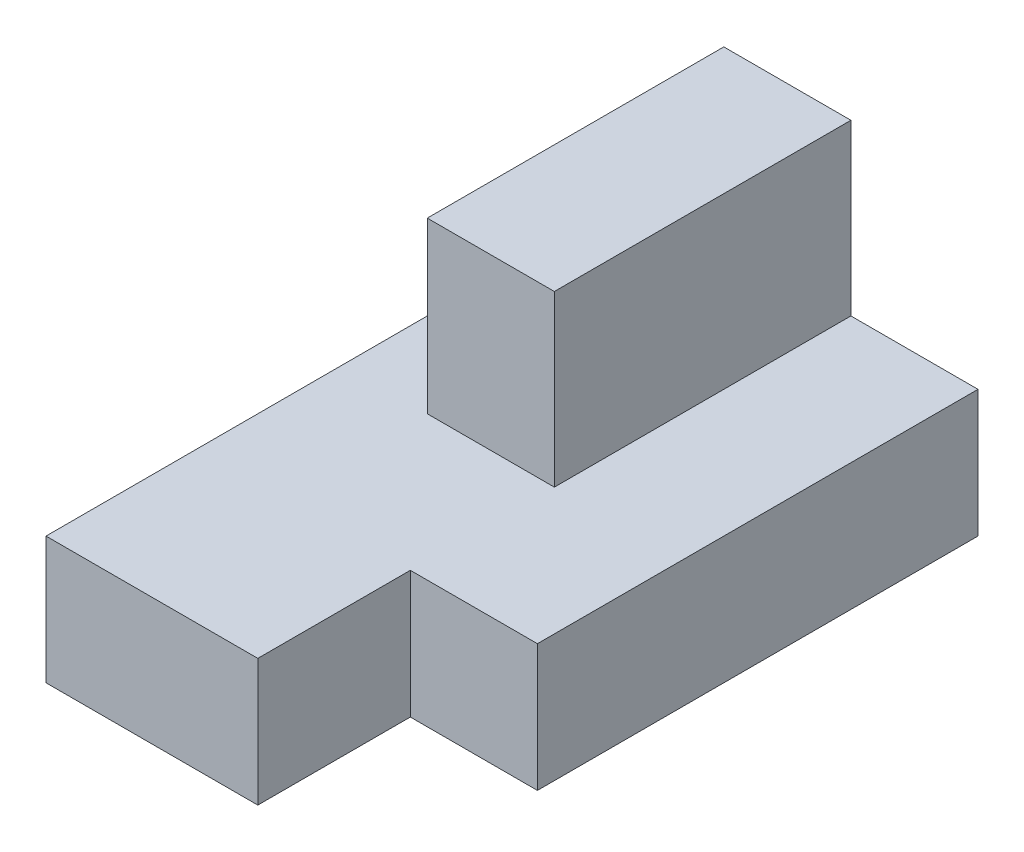
SolidWorks part; units mm, degrees
ref_plane "Ön Düzlem" through (0, 0, 0) normal (0, 0, 1) x (1, 0, 0)
ref_plane "Üst Düzlem" through (0, 0, 0) normal (0, 1, 0) x (1, 0, 0)
ref_plane "Sağ Düzlem" through (0, 0, 0) normal (1, 0, 0) x (0, 0, -1)
sketch "Çizim1" plane through (0, 0, 0) normal (0, 1, 0) x (1, 0, 0)
  line L0 (5, -35) -> (5, -17)
  line L1 (-20, 35) -> (20, 35)
  line L2 (-20, 35) -> (-20, -35)
  line L3 (-20, -35) -> (5, -35)
  line L4 (20, 35) -> (20, -17)
  line L7 (5, -17) -> (20, -17)
  point P0 (0, 0)
  point P1 (-20, 0)
  point P9 (0, 0)
  point P10 (0, 0)
  point P11 (0, -17)
  dimension "D1" = 15
  dimension "D2" = 40
  dimension "D3" = 70
  dimension "D4" = 18
  dimension "D5" = 20
extrude "Yükseklik-Ekstrüzyon1" add sketch "Çizim1" along normal blind 15
sketch "Çizim2" plane through (0, 15, 0) normal (0, 1, 0) x (1, 0, 0)
  line L0 (20, 35) -> (-20, 35) construction
  line L1 (-10, 35) -> (5, 35)
  line L2 (-10, 35) -> (-10, 0)
  line L3 (-10, 0) -> (5, 0)
  line L4 (5, 35) -> (5, 0)
  line L5 (-20, 35) -> (-20, -35) construction
  dimension "D1" = 15
  dimension "D2" = 10
  dimension "D3" = 35
extrude "Yükseklik-Ekstrüzyon2" add sketch "Çizim2" along normal blind 20
